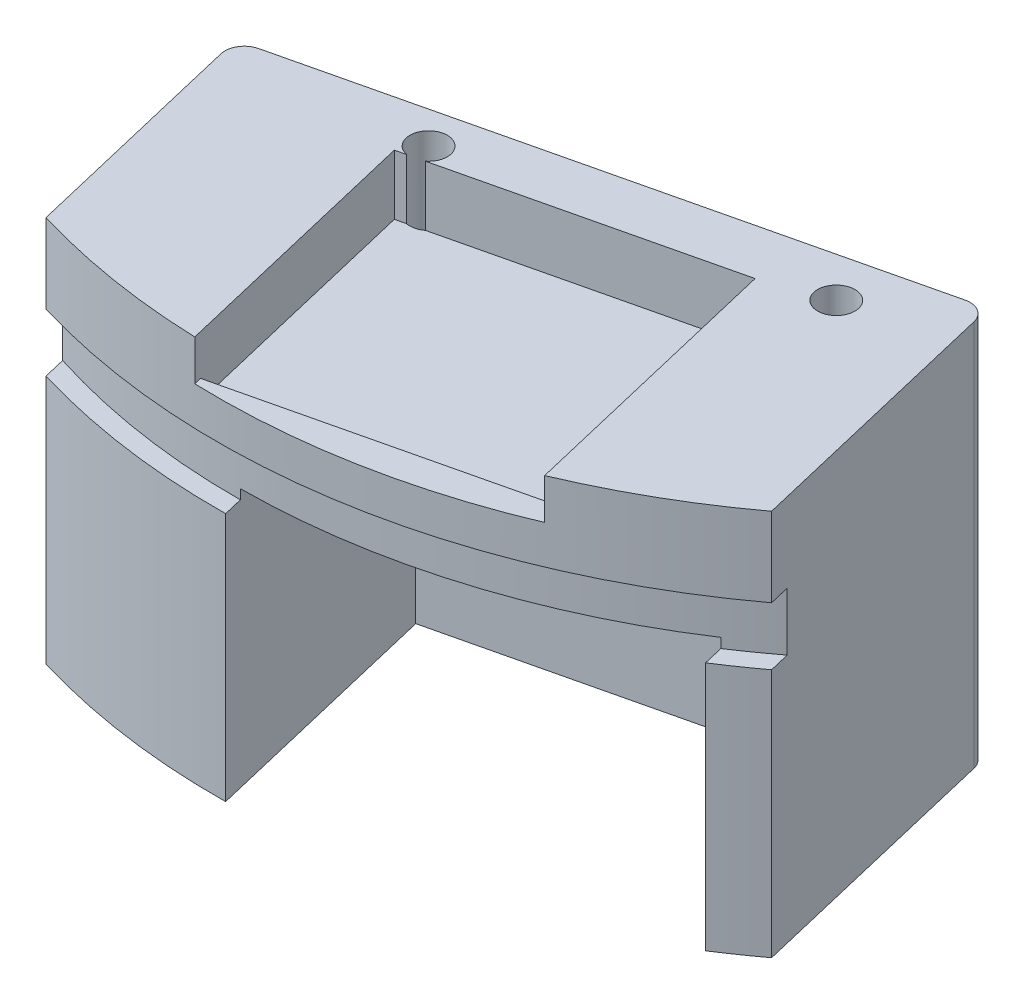
SolidWorks part; units mm, degrees
ref_plane "Front Plane" through (0, 0, 0) normal (0, 0, 1) x (1, 0, 0)
ref_plane "Top Plane" through (0, 0, 0) normal (0, 1, 0) x (1, 0, 0)
ref_plane "Right Plane" through (0, 0, 0) normal (1, 0, 0) x (0, 0, -1)
sketch "Sketch1" plane through (0, 0, 0) normal (0, 1, 0) x (1, 0, 0)
  line L3 (63.0178, -66.7821) -> (53.4682, -26.5063)
  line L5 (53.4682, -26.5063) -> (-35.8757, -47.6903)
  line L6 (-35.8757, -47.6903) -> (-26.3261, -87.9661)
  arc A0 (-26.3261, -87.9661) -> (63.0178, -66.7821) centre (0, 0) ccw
  dimension "D1" = 91.821
  dimension "D2" = 40.2758
  dimension "D3" = 40.2758
extrude "Boss-Extrude1" add sketch "Sketch1" along normal blind 50.8
sketch "Sketch2" plane through (0, 50.8, 0) normal (0, 1, 0) x (1, 0, 0)
  line L0 (-26.3261, -87.9661) -> (63.0178, -66.7821) construction
  line L1 (63.0178, -66.7821) -> (-35.8757, -47.6903) construction
  line L2 (-26.3261, -87.9661) -> (53.4682, -26.5063) construction
  line L3 (8.7963, -37.0983) -> (21.184, -89.3439) construction
  line L4 (53.4682, -26.5063) -> (-35.8757, -47.6903) construction
  line L5 (21.184, -89.3439) -> (19.4139, -81.8783) construction
  line L6 (19.4139, -81.8783) -> (49.0469, -74.8522)
  line L7 (19.4139, -81.8783) -> (-0.1355, -86.5136)
  line L8 (-0.1355, -86.5136) -> (-6.6402, -59.0802)
  line L9 (-6.6402, -59.0802) -> (42.5422, -47.4188)
  line L10 (42.5422, -47.4188) -> (49.0469, -74.8522)
  line L11 (63.0178, -66.7821) -> (53.4682, -26.5063) construction
  arc A0 (-26.3261, -87.9661) -> (63.0178, -66.7821) centre (0, 0) ccw construction
  dimension "D1" = 50.546
  dimension "D2" = 28.194
  dimension "D3" = 17.8275
  dimension "D4" = 15.4559
extrude "Cut-Extrude1" cut sketch "Sketch2" along normal blind 34.036 from surface at -50.8 starting at face at (14.2806, 0, 60.2287)
sketch "Sketch5" plane through (0, 50.8, 0) normal (0, 1, 0) x (1, 0, 0)
  line L0 (45.8431, -47.0277) -> (57.6691, -44.2236) construction
  line L1 (63.0178, -66.7821) -> (53.4682, -26.5063) construction
  line L2 (57.6691, -44.2236) -> (45.8431, -47.0277) construction
  line L3 (45.8431, -47.0277) -> (41.6422, -29.3104) construction
  line L4 (53.4682, -26.5063) -> (-35.8757, -47.6903) construction
  line L5 (41.6422, -29.3104) -> (57.6691, -44.2236) construction
  line L6 (45.8431, -47.0277) -> (53.4682, -26.5063) construction
  line L7 (55.5686, -35.365) -> (-33.7753, -56.549) construction
  line L8 (-35.8757, -47.6903) -> (-26.3261, -87.9661) construction
  line L10 (-24.0126, -44.8775) -> (-21.9122, -53.7362) construction
sketch "Sketch10" plane through (19.4139, 0, 81.8783) normal (-0.2307, 0, -0.973) x (-0.973, 0, 0.2307)
  line L1 (-30.4546, 0) -> (20.0914, 0)
  line L2 (-30.4546, 0) -> (-30.4546, 34.036)
  line L3 (-30.4546, 34.036) -> (20.0914, 34.036)
  line L4 (20.0914, 0) -> (20.0914, 34.036)
extrude "Cut-Extrude3" cut sketch "Sketch10" against normal through all
sketch "Sketch11" plane through (0, 34.036, 0) normal (0, -1, 0) x (1, 0, 0)
  line L0 (49.6179, 77.2604) -> (42.5422, 47.4188) construction
  line L1 (49.6179, 77.2604) -> (-1.9967, 89.4985) construction
  line L2 (42.5422, 47.4188) -> (-9.0723, 59.6569) construction
  line L3 (-1.9967, 89.4985) -> (-9.0723, 59.6569) construction
  line L4 (42.5422, 47.4188) -> (-6.6402, 59.0802) construction
  line L5 (49.6179, 77.2604) -> (42.5422, 47.4188) construction
  line L6 (42.5422, 47.4188) -> (-1.9967, 89.4985) construction
  line L7 (-1.9967, 89.4985) -> (-9.0723, 59.6569) construction
  line L8 (-9.0723, 59.6569) -> (49.6179, 77.2604) construction
  line L9 (4.1267, 64.0245) -> (32.4556, 56.9722)
  line L10 (4.1267, 64.0245) -> (8.09, 79.945)
  line L11 (32.4556, 56.9722) -> (36.4189, 72.8927)
  line L12 (8.09, 79.945) -> (36.4189, 72.8927)
  line L13 (4.1267, 64.0245) -> (36.4189, 72.8927) construction
  line L14 (32.4556, 56.9722) -> (8.09, 79.945) construction
  point P11 (20.2728, 68.4586)
extrude "Cut-Extrude4" cut sketch "Sketch11" against normal blind 2.54
sketch "Sketch12" plane through (0, 50.8, 0) normal (0, 1, 0) x (1, 0, 0)
  line L0 (21.184, -89.3439) -> (8.7963, -37.0983) construction
  line L1 (53.4682, -26.5063) -> (-35.8757, -47.6903) construction
  line L2 (-3.2104, -90.775) -> (35.0975, -81.692)
  line L3 (35.0975, -81.692) -> (27.1864, -48.327)
  line L4 (27.1864, -48.327) -> (-11.1215, -57.4101)
  line L5 (-11.1215, -57.4101) -> (-3.2104, -90.775)
  arc A0 (-26.3261, -87.9661) -> (63.0178, -66.7821) centre (0, 0) ccw construction
  point P10 (20.2068, -85.2226)
  dimension "D2" = 34.29
  dimension "D3" = 39.37
  dimension "D4" = 24.0665
extrude "Cut-Extrude5" cut sketch "Sketch12" against normal blind 7.874
fillet "Fillet1" radius 2.54 1 edges at (53.4682, 25.4, 26.5063)
fillet "Fillet2" radius 2.54 1 edges at (-35.8757, 25.4, 47.6903)
sketch "Sketch13" plane through (0, 50.8, 0) normal (0, 1, 0) x (1, 0, 0)
  line L0 (55.2848, -34.1679) -> (45.8932, -36.3947) construction
  line L1 (63.0178, -66.7821) -> (54.0542, -28.9778) construction
  line L2 (45.8932, -36.3947) -> (44.0766, -28.7332) construction
  line L3 (56.7929, -82.3642) -> (69.1502, -79.4342)
  line L4 (69.1502, -79.4342) -> (54.9707, -19.6319)
  line L5 (54.9707, -19.6319) -> (-50.5613, -44.6542)
  line L6 (50.9967, -27.0923) -> (-33.4042, -47.1043) construction
  line L7 (45.8932, -36.3947) -> (56.7929, -82.3642)
  line L8 (45.8932, -36.3947) -> (-47.2815, -58.487)
  line L9 (-47.2815, -58.487) -> (-50.5613, -44.6542)
extrude "Cut-Extrude6" cut sketch "Sketch13" against normal through all
sketch "Sketch14" plane through (0, 50.8, 0) normal (0, 1, 0) x (1, 0, 0)
  line L0 (33.7053, -39.2846) -> (34.9923, -45.4677) construction
  line L1 (-34.0591, -55.3519) -> (45.8932, -36.3947) construction
  line L2 (34.9923, -45.4677) -> (-33.0448, -59.6298) construction
  line L3 (-34.0591, -55.3519) -> (-26.3261, -87.9661) construction
  line L5 (45.8932, -36.3947) -> (54.7428, -73.7179) construction
  line L6 (-9.3362, -54.6948) -> (-10.5046, -49.767) construction
  dimension "D1" = 5.0644
  dimension "D2" = 24.2076
  dimension "D3" = 6.3132
  dimension "D4" = 12.7
hole_wizard "#10 (0.1935) Diameter Hole1" positions "Sketch15" profile "Sketch16" hole size "#10" standard "ANSI Inch" end condition through all
sketch "Sketch15" plane through (0, 50.8, 0) normal (0, 1, 0) x (1, 0, 0)
  point P0 (-9.3362, -54.6948)
  point P3 (34.9923, -45.4677)
sketch "Sketch16" plane through (-9.3362, 50.8, 54.6948) normal (1, 0, 0) x (0, 0, 1)
  line L0 (0, 0) -> (0, 50.8)
  line L1 (0, 50.8) -> (2.4574, 50.8)
  line L2 (2.4574, 50.8) -> (2.4574, 0)
  line L5 (2.4574, 0) -> (0, 0)
  line L11 (0, -6.35) -> (0, 107.95) construction
  dimension "Thru Hole Dia." = 4.9149
  dimension "Thru Hole Depth" = 50.8
fillet "Fillet3" radius 2.54 2 edges at (-34.0591, 25.4, 55.3519) (45.8932, 25.4, 36.3947)
sketch "Sketch17" plane through (0, 50.8, 0) normal (0, 1, 0) x (1, 0, 0)
  line L0 (-11.1215, -57.4101) -> (-3.2104, -90.775) construction
  line L1 (-5.2878, -82.0135) -> (33.0201, -72.9304)
  line L2 (-5.2878, -82.0135) -> (-1.0586, -99.8502)
  line L3 (-1.0586, -99.8502) -> (37.2493, -90.7672)
  line L4 (33.0201, -72.9304) -> (37.2493, -90.7672)
  line L5 (35.0975, -81.692) -> (27.1864, -48.327) construction
extrude "Cut-Extrude7" cut sketch "Sketch17" against normal offset from surface (5.334 mm away) 2.54 up to face at (5.0602, 42.926, 65.3591)
ref_plane "Plane1" through (1.1213, 0, 91.8142) normal (0.0122, 0, 0.9999) x (0.9999, 0, -0.0122)
ref_plane "Plane2" through (0, 0, 0) normal (0.9999, 0, -0.0122) x (0, 1, 0)
sketch "Sketch18" plane through (0, 0, 0) normal (0.9999, 0, -0.0122) x (0, 1, 0)
  line L0 (27.94, 91.821) -> (-27.94, 91.821) construction
  line L1 (32.766, 91.821) -> (40.386, 91.821)
  line L2 (32.766, 91.821) -> (32.766, 89.281)
  line L3 (32.766, 89.281) -> (40.386, 89.281)
  line L4 (40.386, 91.821) -> (40.386, 89.281)
  line L5 (34.036, 91.821) -> (34.036, 77.8605) construction
  dimension "D1" = 1.27
  dimension "D2" = 7.62
  dimension "D3" = 2.54
ref_axis "Axis1" through (0, 50.8, 0) along (0, -1, 0)
revolve "Cut-Revolve1" cut sketch "Sketch18" angle 360 about axis through (0, 50.8, 0) along (0, -1, 0)
equation "\"D2@Sketch12\"=1.45in-.1"
equation "\"D4@Sketch2\"=0.4785in+.13"
equation "\"D4@Sketch12\"=0.775in+.1725"
